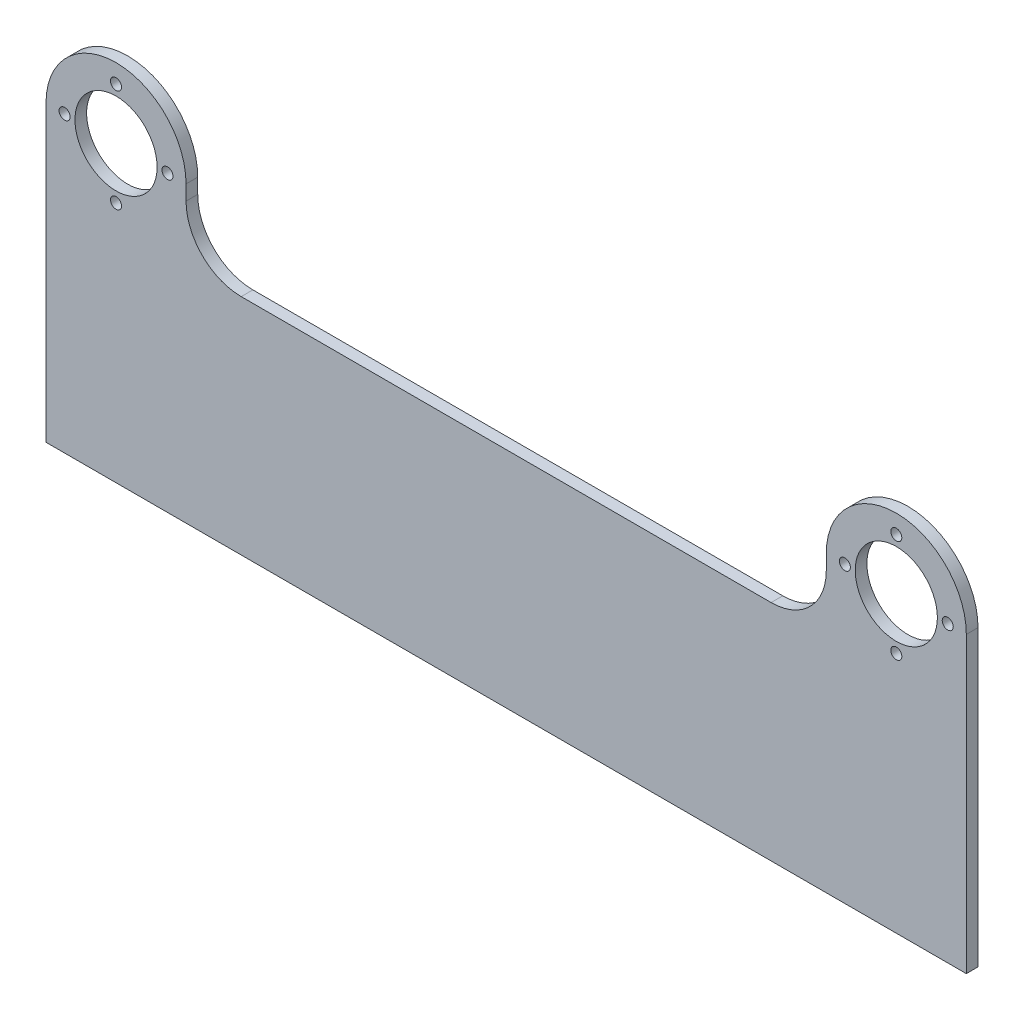
SolidWorks part; units mm, degrees
ref_plane "Front Plane" through (0, 0, 0) normal (0, 0, 1) x (1, 0, 0)
ref_plane "Top Plane" through (0, 0, 0) normal (0, 1, 0) x (1, 0, 0)
ref_plane "Right Plane" through (0, 0, 0) normal (1, 0, 0) x (0, 0, -1)
sketch "Sketch1" plane through (0, 0, 0) normal (0, 0, 1) x (1, 0, 0)
  line L0 (-19.05, -19.05) -> (-19.05, 0)
  line L1 (34.05, -19.05) -> (178.2, -19.05)
  line L2 (-19.05, -19.05) -> (-19.05, -79.9255)
  line L3 (-19.05, -79.9255) -> (231.3, -79.9255)
  line L4 (231.3, -19.05) -> (231.3, -79.9255)
  line L5 (19.05, 0) -> (19.05, -4.05)
  line L6 (193.2, 0) -> (193.2, -4.05)
  line L7 (231.3, 0) -> (231.3, -19.05)
  arc A0 (19.05, 0) -> (-19.05, 0) centre (0, 0) ccw
  arc A1 (231.3, 0) -> (193.2, 0) centre (212.25, 0) ccw
  circle A2 centre (0, 0) radius 11.176
  circle A3 centre (212.25, 0) radius 11.176
  circle A6 centre (0, 13.9954) radius 1.5
  circle A7 centre (212.25, 13.9954) radius 1.5
  circle A8 centre (13.9954, 0) radius 1.5
  circle A9 centre (0, -13.9954) radius 1.5
  circle A10 centre (-13.9954, 0) radius 1.5
  circle A11 centre (198.2546, 0) radius 1.5
  circle A12 centre (212.25, -13.9954) radius 1.5
  circle A13 centre (226.2454, 0) radius 1.5
  arc A14 (193.2, -4.05) -> (178.2, -19.05) centre (178.2, -4.05) cw
  arc A15 (19.05, -4.05) -> (34.05, -19.05) centre (34.05, -4.05) ccw
  point P22 (0, 0)
  point P29 (212.25, 0)
  dimension "D2" = 38.1
  dimension "D3" = 38.1
  dimension "D4" = 4
  dimension "D6" = 15
  dimension "D1" = 212.25
  dimension "D5" = 4
extrude "Boss-Extrude1" add sketch "Sketch1" along normal blind 3.175
